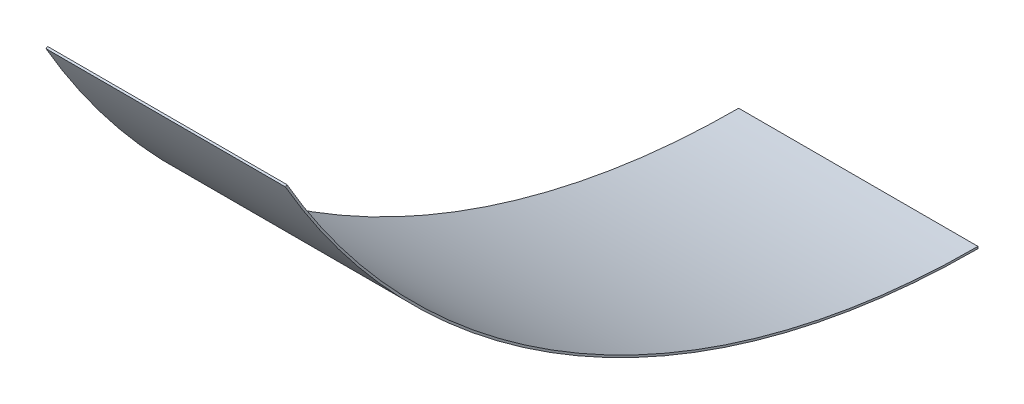
SolidWorks part; units mm, degrees
ref_plane "Front" through (0, 0, 0) normal (0, 0, 1) x (1, 0, 0)
ref_plane "Top" through (0, 0, 0) normal (0, 1, 0) x (1, 0, 0)
ref_plane "Right" through (0, 0, 0) normal (1, 0, 0) x (0, 0, -1)
sketch "Sketch1" plane through (0, 0, 0) normal (0, 0, 1) x (1, 0, 0)
  line L0 (0, 50.9359) -> (-18.4155, 50.9359) construction
  line L1 (0, 0) -> (-15.24, 0)
  line L2 (0, 0) -> (0, 0.127)
  line L3 (0, 0.127) -> (-15.24, 0.127)
  line L4 (-15.24, 0) -> (-15.24, 0.127)
  dimension "D1" = 0.127
  dimension "D2" = 15.24
  dimension "D3" = 50.9359
revolve "Revolve1" add sketch "Sketch1" angle 60 about L0
